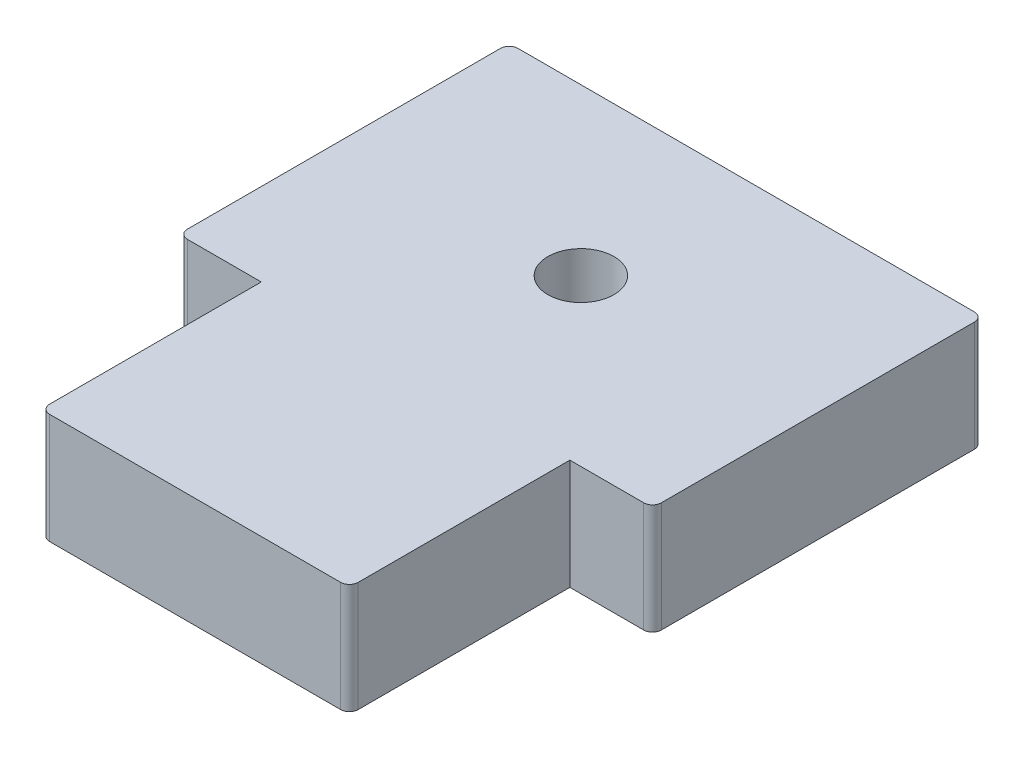
SolidWorks part; units mm, degrees
ref_plane "Front Plane" through (0, 0, 0) normal (0, 0, 1) x (1, 0, 0)
ref_plane "Top Plane" through (0, 0, 0) normal (0, 1, 0) x (1, 0, 0)
ref_plane "Right Plane" through (0, 0, 0) normal (1, 0, 0) x (0, 0, -1)
sketch "Sketch1" plane through (0, 0, 0) normal (0, 1, 0) x (1, 0, 0)
  line L0 (-140, -150) -> (-140, -350)
  line L1 (-215, 150) -> (215, 150)
  line L2 (-215, 150) -> (-215, -150)
  line L3 (-215, -150) -> (-140, -150)
  line L4 (215, 150) -> (215, -150)
  line L5 (-215, 150) -> (215, -150) construction
  line L6 (-215, -150) -> (215, 150) construction
  line L7 (-140, -350) -> (140, -350)
  line L8 (140, -350) -> (140, -150)
  line L9 (140, -150) -> (215, -150)
  point P0 (0, 0)
  dimension "D1" = 300
  dimension "D2" = 75
  dimension "D3" = 75
  dimension "D4" = 200
  dimension "D5" = 430
extrude "Boss-Extrude1" add sketch "Sketch1" along normal blind 100
sketch "Sketch2" plane through (0, 100, 0) normal (0, 1, 0) x (1, 0, 0)
  circle A0 centre (0, 0) radius 30
  dimension "D1" = 60
fillet "Fillet2" radius 8 6 edges at (-215, 50, -150) (-215, 50, 150) (215, 50, -150) (215, 50, 150) (-140, 50, 350) (140, 50, 350)
extrude "Cut-Extrude1" cut sketch "Sketch2" against normal blind 80
